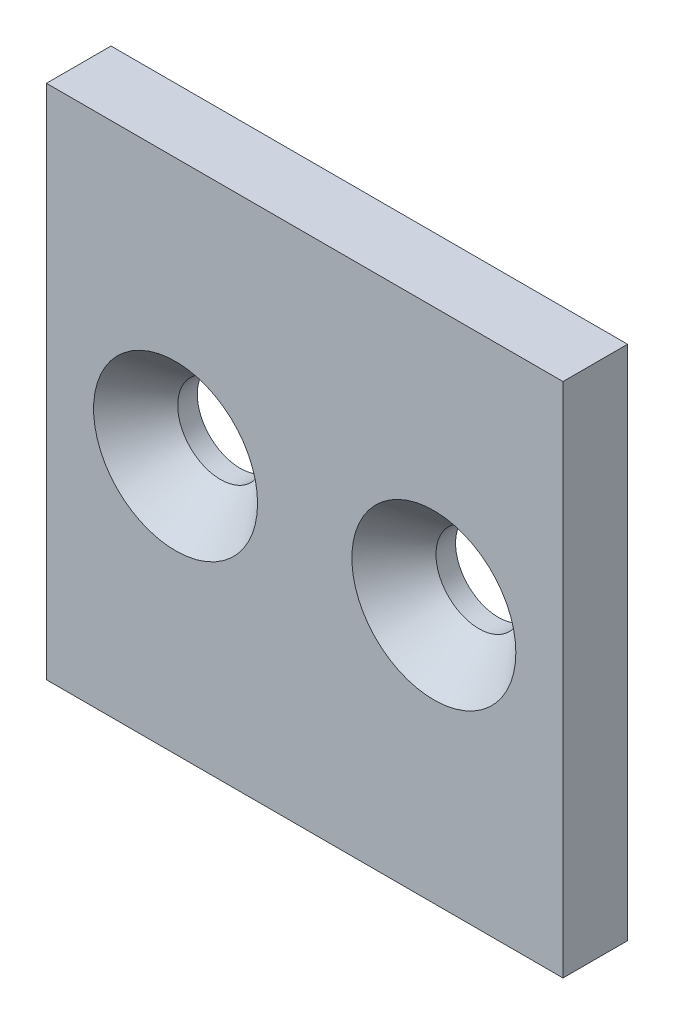
SolidWorks part; units mm, degrees
ref_plane "Front Plane" through (0, 0, 0) normal (0, 0, 1) x (1, 0, 0)
ref_plane "Top Plane" through (0, 0, 0) normal (0, 1, 0) x (1, 0, 0)
ref_plane "Right Plane" through (0, 0, 0) normal (1, 0, 0) x (0, 0, -1)
sketch "Sketch1" plane through (0, 0, 0) normal (0, 0, 1) x (1, 0, 0)
  line L1 (-25.4, 25.4) -> (25.4, 25.4)
  line L2 (-25.4, 25.4) -> (-25.4, -25.4)
  line L3 (-25.4, -25.4) -> (25.4, -25.4)
  line L4 (25.4, 25.4) -> (25.4, -25.4)
  line L5 (-25.4, 25.4) -> (25.4, -25.4) construction
  line L6 (-25.4, -25.4) -> (25.4, 25.4) construction
  circle A0 centre (-12.7, 0) radius 3.2639
  circle A1 centre (12.7, 0) radius 3.2639
  point P0 (0, 0)
  dimension "D3" = 6.5278
  dimension "D4" = 6.5278
  dimension "D1" = 50.8
  dimension "D2" = 50.8
  dimension "D5" = 25.4
  dimension "D6" = 12.7
extrude "Boss-Extrude1" add sketch "Sketch1" against normal blind 6.35
hole_wizard "CSK for 5/16 Flat Head Machine Screw1" positions "3DSketch1" profile "Sketch2" countersink size "5/16" standard "ANSI Inch"
sketch3d "3DSketch1"
  line L0 (-12.7, 0, -6.35) -> (-12.7, 0, 0) construction
  line L1 (12.7, 0, -6.35) -> (12.7, 0, 0) construction
  circle A0 centre (-12.7, 0, 0) radius 3.2639 construction
  point P0 (-15.6578, 1.38, 0)
  point P4 (-12.7, 0, 3.2639)
  point P5 (-12.7, 0, 0)
  point P9 (12.7, 0, 0)
sketch "Sketch2" plane through (-12.7, 0, 0) normal (1, 0, 0) x (0, -1, 0)
  line L0 (0, 0) -> (0, 35.2995)
  line L1 (0, 35.2995) -> (4.2164, 32.766)
  line L2 (4.2164, 32.766) -> (4.2164, 4.4267)
  line L3 (4.2164, 4.4267) -> (8.0645, 0)
  line L5 (8.0645, 0) -> (0, 0)
  line L6 (-4.2164, 4.4267) -> (-8.0645, 0) construction
  line L10 (0, 35.2995) -> (-4.2164, 32.766) construction
  line L11 (0, -6.35) -> (0, 107.95) construction
  dimension "Hole Dia." = 8.4328
  dimension "Hole Depth" = 32.766
  dimension "Near C'Sink Dia." = 16.129
  dimension "Near C'Sink Angle" = 82
  dimension "Drill Angle" = 118
